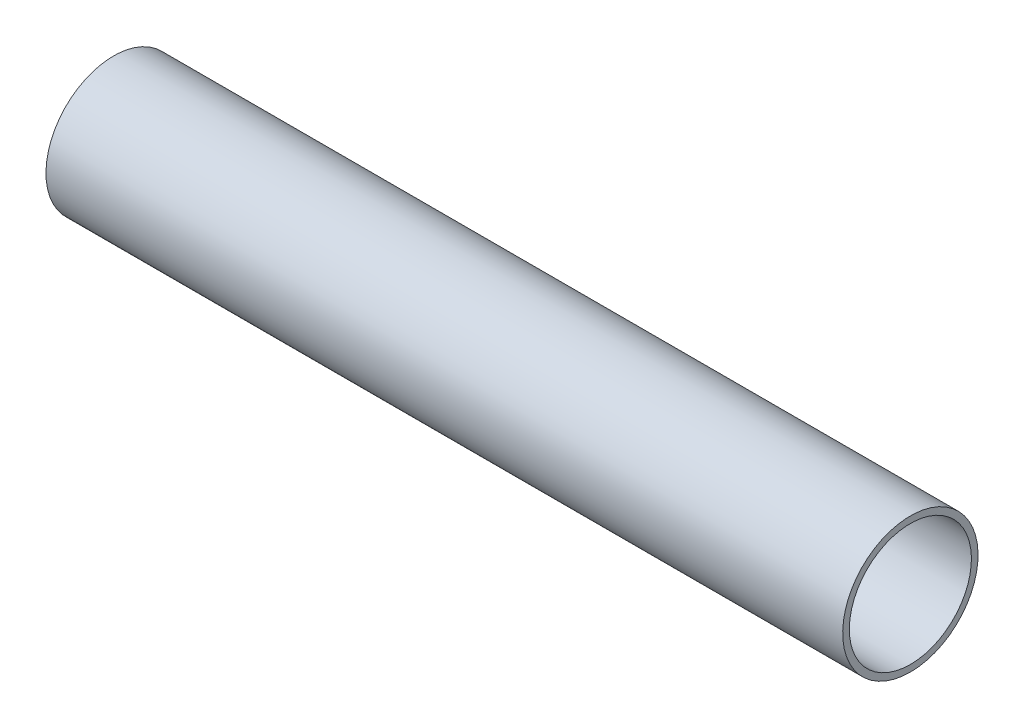
SolidWorks part; units mm, degrees
material "AISI 4130 Steel, normalized at 870C"
ref_plane "Front Plane" through (0, 0, 0) normal (0, 0, 1) x (1, 0, 0)
ref_plane "Top Plane" through (0, 0, 0) normal (0, 1, 0) x (1, 0, 0)
ref_plane "Right Plane" through (0, 0, 0) normal (1, 0, 0) x (0, 0, -1)
sketch "Sketch1" plane through (0, 0, 0) normal (0, 0, 1) x (1, 0, 0)
  line L0 (-666.2482, -0.0004) -> (-582.5982, -0.0004) construction
  line L2 (-670.8982, -6.0004) -> (-670.8982, -6.6504)
  line L3 (-670.8982, -6.6504) -> (-592.5982, -6.6504)
  line L4 (-592.5982, -6.0004) -> (-592.5982, -6.6504)
  line L7 (-666.2482, -0.0004) -> (-582.5982, -0.0004) construction
  line L8 (-670.8982, -6.0004) -> (-592.5982, -6.0004)
  line L9 (-670.8982, -6.7504) -> (-670.8982, 6.7496) construction
  point P0 (-624.4232, -0.0004)
  dimension "BAREL OD" = 13.3
  dimension "BAREL ID" = 12
revolve "Revolve1" add sketch "Sketch1" angle 360 about L0
